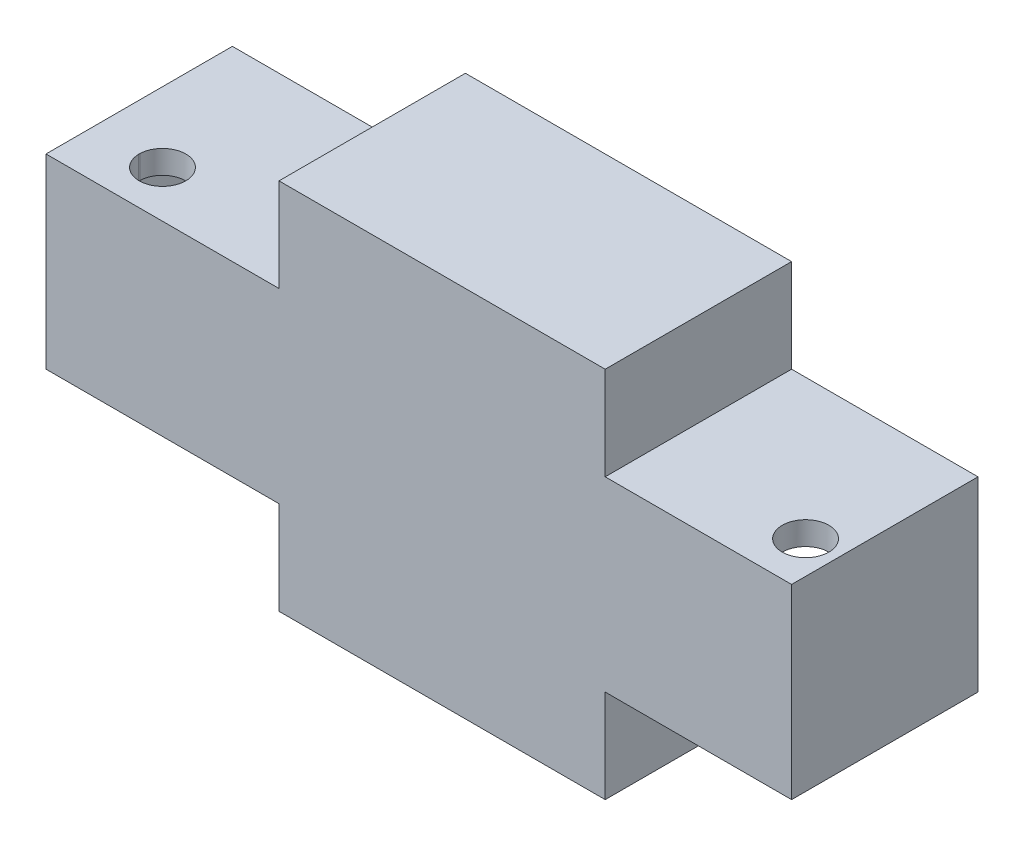
SolidWorks part; units mm, degrees
ref_plane "Front Plane" through (0, 0, 0) normal (0, 0, 1) x (1, 0, 0)
ref_plane "Top Plane" through (0, 0, 0) normal (0, 1, 0) x (1, 0, 0)
ref_plane "Right Plane" through (0, 0, 0) normal (1, 0, 0) x (0, 0, -1)
sketch "Sketch2" plane through (0, 0, 0) normal (0, 0, 1) x (1, 0, 0)
  line L0 (-28.709, -12.7153) -> (-28.709, -38.1153)
  line L1 (-28.709, 63.4847) -> (60.191, 63.4847)
  line L2 (-92.209, 38.0847) -> (-92.209, -12.7153)
  line L3 (-28.709, -38.1153) -> (60.191, -38.1153)
  line L4 (110.991, 38.0847) -> (110.991, -12.7153)
  line L6 (-79.509, -12.7153) -> (-28.709, -12.7153)
  line L7 (-28.709, -12.7153) -> (-28.709, 63.4847)
  line L8 (-92.209, 38.0847) -> (-28.709, 38.0847)
  line L11 (60.191, -38.1153) -> (60.191, 63.4847)
  line L14 (60.191, 38.0847) -> (110.991, 38.0847)
  line L16 (110.991, -12.7153) -> (60.191, -12.7153)
  line L17 (-35.059, -12.7153) -> (-35.059, 38.0847)
  line L18 (-92.209, -12.7153) -> (-79.509, -12.7153)
  line L21 (-73.159, -12.7153) -> (-73.159, 38.0847)
  line L22 (-66.809, -12.7153) -> (-66.809, 38.0847)
  line L24 (-79.509, 38.0847) -> (-79.509, -12.7153)
  line L27 (102.101, -12.7153) -> (102.101, 38.0847)
  line L29 (64.001, 38.0847) -> (64.001, -12.7153)
  line L32 (95.751, -12.7153) -> (95.751, 38.0847)
  line L34 (108.451, 38.0847) -> (108.451, -12.7153)
  dimension "D1" = 63.5
  dimension "D2" = 50.8
  dimension "D3" = 6.35
  dimension "D4" = 50.8
  dimension "D5" = 25.4
  dimension "D6" = 6.35
  dimension "D7" = 38.1
  dimension "D8" = 6.35
  dimension "D9" = 88.9
  dimension "D10" = 3.81
  dimension "D11" = 38.1
  dimension "D12" = 6.35
  dimension "D13" = 6.35
extrude "Boss-Extrude2" add sketch "Sketch2" along normal blind 73.66 contours L32 L16 L27 L14 | L34 L14 L27 L16 | L14 L34 L16 L4 | L16 L32 L14 L29 | L29 L14 L11 L16 | L3 L11 L1 L7 L0 | L17 L6 L7 L8 | L22 L6 L17 L8 | L6 L22 L8 L21 | L8 L24 L6 L21 | L24 L8 L2 L18
sketch "Sketch3" plane through (0, 0, 73.66) normal (0, 0, 1) x (1, 0, 0)
  line L0 (-28.709, -12.7153) -> (-35.059, -12.7153)
  line L1 (-92.209, -12.7153) -> (-28.709, -12.7153) construction
  line L2 (-35.059, -12.7153) -> (-73.159, -12.7153)
  line L3 (-73.159, -12.7153) -> (-73.159, 38.0847)
  line L4 (-92.209, 38.0847) -> (-28.709, 38.0847) construction
  line L5 (-73.159, 38.0847) -> (-35.059, 38.0847)
  line L6 (-35.059, 38.0847) -> (-35.059, -12.7153)
  line L7 (-73.159, -12.7153) -> (-66.809, -12.7153)
  line L8 (-66.809, -12.7153) -> (-66.809, 38.0847)
  line L9 (-66.809, 38.0847) -> (-79.509, 38.0847)
  line L10 (-79.509, 38.0847) -> (-79.509, -12.7153)
  line L11 (-79.509, -12.7153) -> (-66.809, -12.7153)
  line L12 (-35.059, 38.0847) -> (-28.709, 38.0847)
  line L13 (60.191, -12.7153) -> (64.001, -12.7153)
  line L14 (110.991, -12.7153) -> (60.191, -12.7153) construction
  line L15 (64.001, -12.7153) -> (102.101, -12.7153)
  line L16 (102.101, -12.7153) -> (108.451, -12.7153)
  line L17 (108.451, -12.7153) -> (108.451, 38.0847)
  line L18 (60.191, 38.0847) -> (110.991, 38.0847) construction
  line L19 (108.451, 38.0847) -> (102.101, 38.0847)
  line L20 (102.101, 38.0847) -> (95.751, 38.0847)
  line L21 (95.751, 38.0847) -> (95.751, -12.7153)
  line L22 (95.751, -12.7153) -> (108.451, -12.7153)
  line L23 (102.101, 38.0847) -> (102.101, -12.7153)
  line L24 (64.001, -12.7153) -> (64.001, 38.0847)
  line L25 (64.001, 38.0847) -> (60.191, 38.0847)
  dimension "D1" = 6.35
  dimension "D2" = 38.1
  dimension "D3" = 6.35
  dimension "D4" = 6.35
  dimension "D5" = 3.81
  dimension "D6" = 38.1
  dimension "D7" = 6.35
  dimension "D8" = 6.35
sketch "Sketch4" plane through (0, 38.0847, 0) normal (0, 1, 0) x (1, 0, 0)
  line L0 (-79.5052, -76.2) -> (-79.5052, 0)
  line L1 (-92.209, 0) -> (-28.709, 0) construction
  line L2 (-79.5052, -76.2) -> (-73.159, -73.66)
  line L5 (-73.159, -73.66) -> (-66.809, -73.66)
  line L6 (-79.509, -73.66) -> (-66.809, -73.66) construction
  line L7 (-73.159, -73.66) -> (-66.809, -73.66) construction
  line L8 (-66.809, -73.66) -> (-66.809, 0)
  line L9 (-66.809, 0) -> (-73.159, 0)
  line L10 (-73.159, 0) -> (-79.5052, 0)
  line L11 (-73.159, 0) -> (-73.159, -73.66)
  line L12 (-35.059, -73.66) -> (-35.059, 0)
  line L13 (-35.059, 0) -> (-28.709, 0)
  line L14 (64.001, -73.66) -> (64.001, 0)
  line L15 (60.191, 0) -> (110.991, 0) construction
  line L16 (64.001, 0) -> (60.191, 0)
  line L17 (95.751, -73.66) -> (95.751, 0)
  line L18 (95.751, -73.66) -> (102.101, -73.66)
  line L19 (102.101, -73.66) -> (108.451, -73.66)
  line L20 (108.451, -73.66) -> (108.451, 0)
  line L21 (108.451, 0) -> (102.101, 0)
  line L22 (102.101, 0) -> (95.751, 0)
  line L23 (102.101, 0) -> (102.101, -73.66)
  line L24 (-73.159, -73.66) -> (-73.159, -60.96)
  line L25 (102.101, -73.66) -> (102.101, -60.96)
  circle A0 centre (-73.159, -60.96) radius 6.35
  circle A1 centre (102.101, -60.96) radius 6.35
  dimension "D1" = 76.2
  dimension "D2" = 12.7
  dimension "D3" = 12.7
extrude "Cut-Extrude2" cut sketch "Sketch4" against normal through all both and the other way through all contours L11 A0 | L11 A0 L0 | L23 A1 | L23 A1
sketch "Sketch5" plane through (0, 0, 0) normal (0, 0, -1) x (-1, 0, 0)
  line L0 (-60.191, -38.1153) -> (-60.191, -12.7153) construction
  line L1 (-110.991, -12.7153) -> (-60.191, -12.7153) construction
  line L2 (-110.991, 38.0847) -> (-110.991, -12.7153) construction
  line L3 (-60.191, 38.0847) -> (-110.991, 38.0847) construction
  line L4 (-60.191, 38.0847) -> (-60.191, 63.4847) construction
  line L5 (28.709, 63.4847) -> (-60.191, 63.4847) construction
  line L6 (28.709, 38.0847) -> (28.709, 63.4847) construction
  line L7 (92.209, 38.0847) -> (28.709, 38.0847) construction
  line L8 (92.209, 38.0847) -> (92.209, -12.7153) construction
  line L9 (92.209, -12.7153) -> (28.709, -12.7153) construction
  line L10 (28.709, -38.1153) -> (28.709, -12.7153) construction
  line L11 (28.709, -38.1153) -> (-60.191, -38.1153) construction
  line L12 (-60.191, -38.1153) -> (-60.191, -12.7153)
  line L13 (-110.991, -12.7153) -> (-60.191, -12.7153)
  line L14 (-110.991, 38.0847) -> (-110.991, -12.7153)
  line L15 (-60.191, 38.0847) -> (-110.991, 38.0847)
  line L16 (-60.191, 38.0847) -> (-60.191, 63.4847)
  line L17 (28.709, 63.4847) -> (-60.191, 63.4847)
  line L18 (28.709, 38.0847) -> (28.709, 63.4847)
  line L19 (92.209, 38.0847) -> (28.709, 38.0847)
  line L20 (92.209, 38.0847) -> (92.209, -12.7153)
  line L21 (92.209, -12.7153) -> (28.709, -12.7153)
  line L22 (28.709, -38.1153) -> (28.709, -12.7153)
  line L23 (28.709, -38.1153) -> (-60.191, -38.1153)
extrude "Cut-Extrude3" cut sketch "Sketch5" against normal blind 22.86 contours L12 L13 L14 L15 L16 L17 L18 L19 L20 L21 L22 L23
sketch "Sketch8" plane through (0, 0, 22.86) normal (0, 0, -1) x (-1, 0, 0)
  line L0 (-104.641, -6.3653) -> (-53.841, -6.3653)
  line L1 (-110.991, 38.0847) -> (-110.991, -12.7153) construction
  line L4 (85.859, 31.7347) -> (22.359, 31.7347)
  line L5 (-110.991, 31.7347) -> (-110.991, -6.3653)
  line L7 (85.859, -6.3653) -> (85.859, 31.7347)
  line L8 (-104.641, -6.3653) -> (-104.641, 31.7347)
  line L9 (22.359, -6.3653) -> (22.359, -31.7653)
  line L12 (-53.841, -31.7653) -> (-53.841, -6.3653)
  line L15 (22.359, 57.1347) -> (22.359, 31.7347)
  line L16 (22.359, -31.7653) -> (-53.841, -31.7653)
  line L17 (22.359, 57.1347) -> (-53.841, 57.1347)
  line L18 (22.359, -6.3653) -> (85.859, -6.3653)
  line L19 (-53.841, 31.7347) -> (-53.841, 57.1347)
  line L20 (-53.841, 31.7347) -> (-104.641, 31.7347)
extrude "Cut-Extrude4" cut sketch "Sketch8" against normal blind 38.1 contours L4 L15 L17 L19 L20 L8 L0 L12 L16 L9 L18 L7
